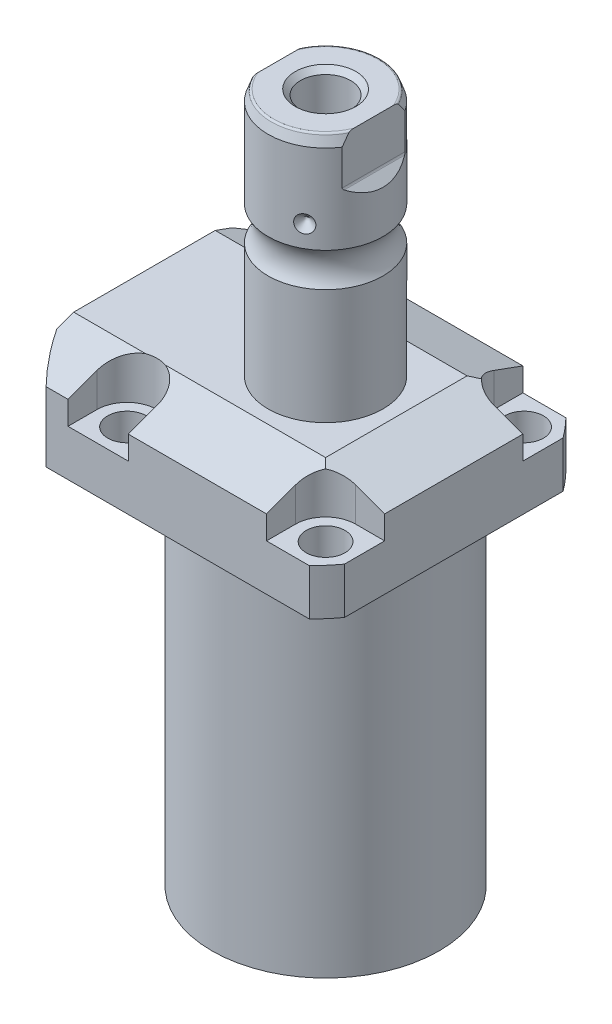
SolidWorks part; units mm, degrees
material "Alloy Steel"
ref_plane "Front Plane" through (0, 0, 0) normal (0, 0, 1) x (1, 0, 0)
ref_plane "Top Plane" through (0, 0, 0) normal (0, 1, 0) x (1, 0, 0)
ref_plane "Right Plane" through (0, 0, 0) normal (1, 0, 0) x (0, 0, -1)
sketch "Sketch1" plane through (0, 0, 0) normal (0, -1, 0) x (0, 0, 1)
  line L0 (-35.433, 50.063) -> (35.433, 50.063)
  line L1 (35.433, 50.063) -> (35.433, -35.433)
  line L2 (35.433, -35.433) -> (-35.433, -35.433)
  line L3 (-35.433, -35.433) -> (-35.433, 50.063)
  line L4 (0, 0) -> (0, -60.6467) construction
  dimension "D1" = 35.433
  dimension "D2" = 85.496
  dimension "D3" = 70.866
extrude "Extrude1" add sketch "Sketch1" against normal blind 121.9708
sketch "Sketch2" plane through (0, 0, 0) normal (0, -1, 0) x (1, 0, 0)
  circle A0 centre (-5.4102, 0) radius 50.8
  dimension "D1" = 101.6
  dimension "D2" = 5.4102
extrude "Cut-Extrude1" cut sketch "Sketch2" against normal through all flip side to cut
sketch "Sketch3" plane through (0, 0, 0) normal (1, 0, 0) x (0, 0, -1)
  line L0 (31.3945, 0) -> (31.3945, 96.9518)
  line L1 (31.3945, 96.9518) -> (76.5937, 96.9518)
  line L2 (76.5937, 96.9518) -> (76.5937, 0)
  line L3 (76.5937, 0) -> (31.3945, 0)
  line L4 (0, -93.345) -> (0, 4.445) construction
  line L5 (24.2233, 0) -> (-24.2233, 0) construction
  dimension "D1" = 62.789
  dimension "D2" = 153.1874
  dimension "D3" = 96.9518
revolve "Cut-Revolve1" cut sketch "Sketch3" angle 360 about L4
fillet "Fillet1" radius 0.381 1 edges at (0, 96.9518, -31.3945)
sketch "Sketch4" plane through (0, 121.9708, 0) normal (0, 1, 0) x (-1, 0, 0)
  line L0 (-35.433, -30.2072) -> (-35.433, 30.2072) construction
  line L1 (41.8127, 35.433) -> (-30.9923, 35.433) construction
  line L2 (-19.1008, -35.433) -> (-19.1008, -27.432)
  line L3 (-35.433, -35.433) -> (-19.1008, -35.433)
  line L4 (-35.433, -19.1008) -> (-35.433, -35.433)
  line L5 (-27.432, -19.1008) -> (-35.433, -19.1008)
  line L6 (35.7632, -35.433) -> (19.1008, -35.433)
  line L7 (19.1008, 35.433) -> (19.1008, 27.432)
  line L8 (35.7632, 35.433) -> (35.7632, 27.432)
  line L9 (35.7632, 35.433) -> (19.1008, 35.433)
  line L10 (-27.432, 19.1008) -> (-35.433, 19.1008)
  line L11 (-35.433, 19.1008) -> (-35.433, 35.433)
  line L12 (-35.433, 35.433) -> (-19.1008, 35.433)
  line L13 (-19.1008, 35.433) -> (-19.1008, 27.432)
  line L14 (-48.9217, 0) -> (49.4551, 0) construction
  line L15 (35.7632, -35.433) -> (35.7632, -27.432)
  line L16 (19.1008, -35.433) -> (19.1008, -27.432)
  arc A0 (19.1008, -27.432) -> (35.7632, -27.432) centre (27.432, -27.432) cw
  arc A1 (-27.432, -19.1008) -> (-19.1008, -27.432) centre (-27.432, -27.432) cw
  arc A2 (-27.432, 19.1008) -> (-19.1008, 27.432) centre (-27.432, 27.432) ccw
  arc A3 (19.1008, 27.432) -> (35.7632, 27.432) centre (27.432, 27.432) ccw
  dimension "D2" = 8.3312
  dimension "D1" = 27.432
  dimension "D3" = 27.432
  dimension "D4" = 54.864
extrude "Cut-Extrude2" cut sketch "Sketch4" against normal blind 12.243
sketch "Sketch5" plane through (0, 0, 0) normal (1, 0, 0) x (0, 0, -1)
  line L0 (-19.558, 121.9708) -> (-35.433, 116.1928)
  line L1 (0, 0) -> (0, 154.1081) construction
  line L2 (-19.558, 121.9708) -> (-35.433, 121.9708)
  line L3 (-35.433, 121.9708) -> (-35.433, 116.1928)
  dimension "D1" = 15.875
  dimension "D2" = 20
extrude "Cut-Extrude9" cut sketch "Sketch5" against normal through all and the other way through all
mirror "Mirror1" about plane through (0, 0, 0) normal (0, 0, 1) of "Cut-Extrude9"
sketch "Sketch9" plane through (0, 0, 0) normal (0, 0, 1) x (1, 0, 0)
  line L0 (19.558, 121.9708) -> (35.433, 116.1928)
  line L1 (35.433, 116.1928) -> (35.433, 121.9708)
  line L2 (35.433, 121.9708) -> (19.558, 121.9708)
  dimension "D1" = 15.875
  dimension "D2" = 20
extrude "Cut-Extrude7" cut sketch "Sketch9" against normal through all and the other way through all
ref_plane "Plane14" through (-35.0774, 0, 0) normal (1, 0, 0) x (0, 0, -1)
sketch "Sketch20" plane through (-35.0774, 88.9, -18.1102) normal (1, 0, 0) x (0, 1, 0)
  line L0 (-88.9, 18.1102) -> (39.8401, 18.1102) construction
  line L1 (-7.2797, 32.639) -> (36.9042, 32.639) construction
  line L2 (8.0518, 38.3413) -> (9.4996, 38.3413)
  line L3 (8.0518, -6.1131) -> (8.0518, 42.3335) construction
  line L4 (9.4996, 38.3413) -> (9.4996, 35.8902)
  line L5 (9.4996, 35.8902) -> (10.5156, 35.8902)
  line L6 (10.5156, 35.8902) -> (10.5156, 33.8836)
  line L7 (10.5156, 33.8836) -> (21.4884, 33.8836)
  line L8 (21.4884, 33.8836) -> (21.4884, 32.639)
  line L9 (21.4884, 32.639) -> (8.0518, 32.639)
  line L10 (8.0518, 38.3413) -> (8.0518, 32.639)
  dimension "D1" = 14.5288
  dimension "D2" = 11.4046
  dimension "D3" = 1.4478
  dimension "D4" = 6.5024
  dimension "D5" = 1.016
  dimension "D6" = 2.4892
  dimension "D7" = 10.9728
revolve "Cut-Revolve4" cut sketch "Sketch20" angle 360 about L1
mirror "Mirror10" about plane through (0, 0, 0) normal (0, 0, 1) of "Cut-Revolve4"
sketch "Sketch10" plane through (-35.0774, 88.9, -18.1102) normal (1, 0, 0) x (0, 1, 0)
  line L0 (-1.0325, 3.5814) -> (1.5659, 3.5814) construction
  line L1 (21.4884, 4.826) -> (10.5156, 4.826) construction
  line L2 (10.5156, 2.3368) -> (21.4884, 2.3368) construction
  line L4 (8.0518, -12.097) -> (8.0518, 48.3174) construction
  circle A0 centre (8.3185, 8.1026) radius 1.1811
  dimension "D1" = 2.3622
  dimension "D2" = 0.2667
  dimension "D3" = 9.0424
revolve "Revolve4" add sketch "Sketch10" angle 360 about L0
mirror "Mirror12" about plane through (0, 0, 0) normal (0, 0, 1) of bodies 135
sketch "Sketch15" plane through (0, 0, 0) normal (1, 0, 0) x (0, 0, -1)
  line L0 (0, 121.9708) -> (15.875, 121.9708)
  line L1 (15.875, 121.9708) -> (15.875, 153.8139)
  line L2 (15.875, 163.2281) -> (15.875, 187.706)
  line L3 (14.8118, 190.627) -> (0, 190.627)
  line L4 (0, 190.627) -> (0, 121.9708)
  line L5 (0, 250.2908) -> (0, 28.9095) construction
  line L6 (19.558, 121.9708) -> (-19.558, 121.9708) construction
  line L7 (14.8118, 190.627) -> (15.875, 187.706)
  line L9 (24.2233, 96.9518) -> (35.433, 96.9518) construction
  arc A0 (15.875, 163.2281) -> (15.875, 153.8139) centre (22.2504, 158.521) ccw
  dimension "D2" = 20
  dimension "D4" = 7.9248
  dimension "D6" = 28.6512
  dimension "D1" = 93.6752
  dimension "D3" = 31.75
  dimension "D5" = 32.106
  dimension "D7" = 2.921
revolve "Revolve3" add sketch "Sketch15" angle 360 about L5
hole_wizard "Hole1" positions "Sketch18" profile "Sketch17" legacy end condition up to next
sketch "Sketch18" plane through (0, 109.7278, 0) normal (0, 1, 0) x (-1, 0, 0)
  arc A0 (35.7632, -27.432) -> (19.1008, -27.432) centre (27.432, -27.432) ccw construction
  arc A1 (19.1008, 27.432) -> (35.7632, 27.432) centre (27.432, 27.432) ccw construction
  arc A2 (-27.432, 19.1008) -> (-19.1008, 27.432) centre (-27.432, 27.432) ccw construction
  arc A3 (-19.1008, -27.432) -> (-27.432, -19.1008) centre (-27.432, -27.432) ccw construction
  point P0 (-27.432, -27.432)
  point P1 (-27.432, 27.432)
  point P3 (27.432, 27.432)
  point P5 (27.432, -27.432)
sketch "Sketch17" plane through (27.432, 109.7278, -27.432) normal (1, 0, 0) x (0, 0, 1)
  line L0 (0, 0) -> (0, 12.776)
  line L1 (0, 12.776) -> (5.3594, 12.776)
  line L2 (5.3594, 12.776) -> (5.3594, 0)
  line L3 (5.3594, 0) -> (0, 0)
  line L4 (0, 110) -> (0, -10) construction
  dimension "Diameter" = 10.7188
  dimension "Depth" = 12.776
chamfer "Chamfer1" distance 0.635 angle 45 2 edges at (-35.0774, 99.4156, 13.2842) (-35.0774, 99.4156, -13.2842)
ref_plane "Plane15" through (0, 109.4486, 0) normal (0, -1, 0) x (1, 0, 0)
sketch "Sketch21" plane through (0, 109.4486, 0) normal (0, -1, 0) x (1, 0, 0)
  line L0 (-57.5495, -12.9794) -> (-2.9353, -12.9794) construction
  line L1 (-50.063, -1.9304) -> (-49.809, -1.9304)
  line L2 (-49.809, -1.9304) -> (-49.809, -6.7564)
  line L3 (-49.809, -6.7564) -> (-47.2563, -7.4404)
  line L4 (-46.6957, -8.001) -> (-30.759, -8.001)
  line L5 (-30.759, -8.001) -> (-30.759, -12.9794)
  line L6 (-30.759, -12.9794) -> (-50.063, -12.9794)
  line L7 (-50.063, 24.2233) -> (-50.063, -24.2233) construction
  line L8 (-50.063, -12.9794) -> (-50.063, -1.9304)
  line L9 (-47.2563, -7.4404) -> (-46.6957, -8.001)
  dimension "D1" = 12.9794
  dimension "D2" = 0.254
  dimension "D3" = 22.098
  dimension "D4" = 45
  dimension "D5" = 2.5527
  dimension "D6" = 9.9568
  dimension "D7" = 19.05
  dimension "D8" = 15
  dimension "D9" = 12.446
revolve "Cut-Revolve5" cut sketch "Sketch21" angle 360 about L0
mirror "Mirror13" about plane through (0, 0, 0) normal (0, 0, 1) of "Cut-Revolve5"
fillet "Fillet2" radius 0.635 1 edges at (0, 190.627, 14.8118)
sketch "Sketch26" plane through (0, 0, 0) normal (0, 0, 1) x (1, 0, 0)
  line L0 (-39.772, 169.189) -> (35.3173, 169.189) construction
  line L1 (-15.875, 171.602) -> (-13.462, 169.189)
  line L2 (-15.875, 187.706) -> (-15.875, 163.2281) construction
  line L3 (-13.462, 169.189) -> (-15.875, 169.189)
  line L4 (-15.875, 169.189) -> (-15.875, 171.602)
  arc A0 (-15.875, 153.8139) -> (-15.875, 163.2281) centre (-22.2504, 158.521) ccw construction
  dimension "D1" = 45
  dimension "D2" = 4.826
  dimension "D3" = 10.668
revolve "Cut-Revolve7" cut sketch "Sketch26" angle 360 about L0
pattern_circular "CirPattern1" count 3 over 360 about axis through (0, 250.2908, 0) along (0, 1, 0) of "Cut-Revolve7"
hole_wizard "Hole2" positions "Sketch28" profile "Sketch27" legacy
sketch "Sketch28" plane through (0, 190.627, 0) normal (0, 1, 0) x (-1, 0, 0)
  circle A0 centre (0, 0) radius 15.875 construction
  point P0 (0, 0)
sketch "Sketch27" plane through (0, 190.627, 0) normal (1, 0, 0) x (0, 0, 1)
  line L0 (0, 0) -> (0, 28.8121)
  line L1 (0, 28.8121) -> (6.9469, 24.638)
  line L2 (6.9469, 24.638) -> (6.9469, 0)
  line L4 (6.9469, 0) -> (0, 0)
  line L6 (0, 28.8121) -> (-6.9469, 24.638) construction
  line L7 (0, -4.2442) -> (0, 117.3081) construction
  dimension "Diameter" = 13.8938
  dimension "Depth" = 24.638
  dimension "Drill Angle" = 118
sketch "Sketch29" plane through (0, 0, 0) normal (0, 0, 1) x (1, 0, 0)
  line L0 (0, 0) -> (0, 192.0172) construction
  line L1 (13.284, 190.627) -> (13.284, 177.927)
  line L2 (14.3672, 190.627) -> (-14.3672, 190.627) construction
  line L3 (13.5072, 177.3882) -> (16.332, 174.5634)
  line L5 (16.332, 174.5634) -> (16.332, 190.627)
  line L6 (16.332, 190.627) -> (13.284, 190.627)
  line L7 (-16.332, 190.627) -> (-13.284, 190.627)
  line L8 (-16.332, 174.5634) -> (-16.332, 190.627)
  line L9 (-13.5072, 177.3882) -> (-16.332, 174.5634)
  line L10 (-13.284, 190.627) -> (-13.284, 177.927)
  arc A0 (13.284, 177.927) -> (13.5072, 177.3882) centre (14.046, 177.927) ccw
  arc A1 (-13.284, 177.927) -> (-13.5072, 177.3882) centre (-14.046, 177.927) cw
  dimension "D2" = 0.762
  dimension "D1" = 45
  dimension "D3" = 26.568
  dimension "D4" = 12.7
  dimension "D5" = 3.048
extrude "Cut-Extrude10" cut sketch "Sketch29" against normal through all and the other way through all
chamfer "Chamfer2" distance 1.4351 angle 45 1 edges at (0, 190.627, 6.9469)
